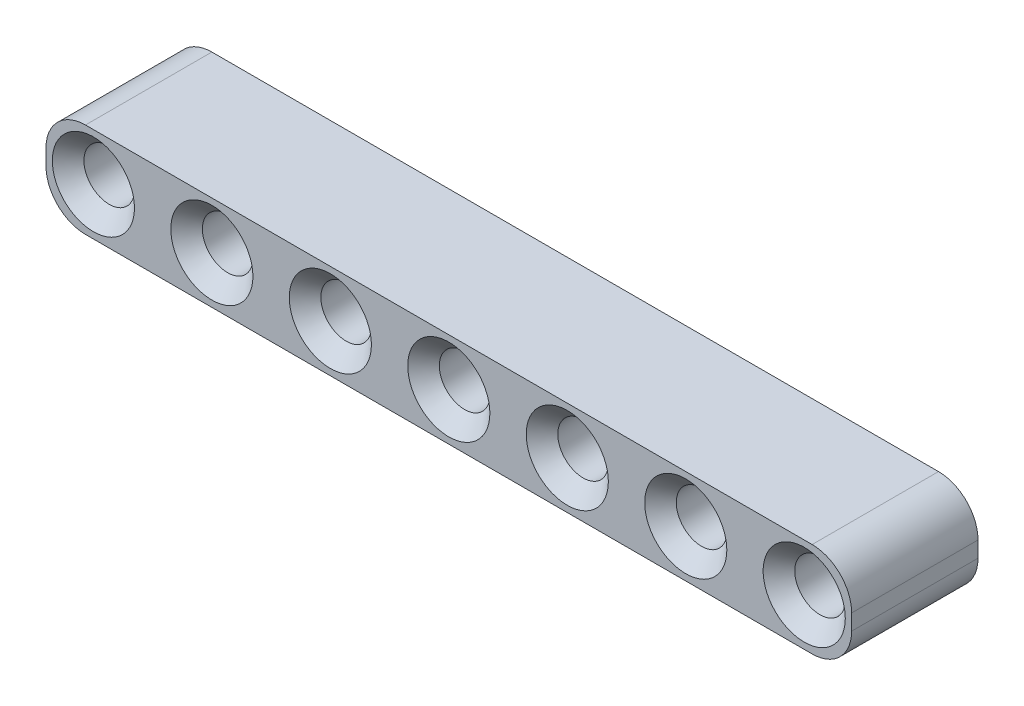
SolidWorks part; units mm, degrees
ref_plane "Front Plane" through (0, 0, 0) normal (0, 0, 1) x (1, 0, 0)
ref_plane "Top Plane" through (0, 0, 0) normal (0, 1, 0) x (1, 0, 0)
ref_plane "Right Plane" through (0, 0, 0) normal (1, 0, 0) x (0, 0, -1)
sketch "Sketch1" plane through (0, 0, 0) normal (0, 0, 1) x (1, 0, 0)
  line L1 (-0.5, 3) -> (45.5, 3)
  line L2 (-3, 0.5) -> (-3, -0.5)
  line L3 (-0.5, -3) -> (45.5, -3)
  line L4 (48, 0.5) -> (48, -0.5)
  circle A0 centre (0, 0) radius 1.6
  arc A1 (45.5, -3) -> (48, -0.5) centre (45.5, -0.5) ccw
  arc A2 (45.5, 3) -> (48, 0.5) centre (45.5, 0.5) cw
  arc A3 (-3, -0.5) -> (-0.5, -3) centre (-0.5, -0.5) ccw
  arc A4 (-0.5, 3) -> (-3, 0.5) centre (-0.5, 0.5) ccw
  circle A5 centre (7.5, 0) radius 1.6
  circle A6 centre (15, 0) radius 1.6
  circle A7 centre (22.5, 0) radius 1.6
  circle A8 centre (30, 0) radius 1.6
  circle A9 centre (37.5, 0) radius 1.6
  circle A10 centre (45, 0) radius 1.6
  point P8 (-3, 0)
  point P14 (-3, -3)
  point P17 (-3, 3)
  dimension "D1" = 3.2
  dimension "D4" = 2.5
  dimension "D2" = 6
  dimension "D3" = 3
  dimension "D6" = 7.5
  dimension "D5" = 7
extrude "Boss-Extrude1" add sketch "Sketch1" along normal blind 8
chamfer "Chamfer1" distance 1 angle 45 14 edges at (46.6, 0, 0) (46.6, 0, 8) (39.1, 0, 0) (39.1, 0, 8) (31.6, 0, 0) (31.6, 0, 8) (24.1, 0, 0) (24.1, 0, 8) (16.6, 0, 0) (16.6, 0, 8) (9.1, 0, 0) (9.1, 0, 8) (1.6, 0, 0) (1.6, 0, 8)
